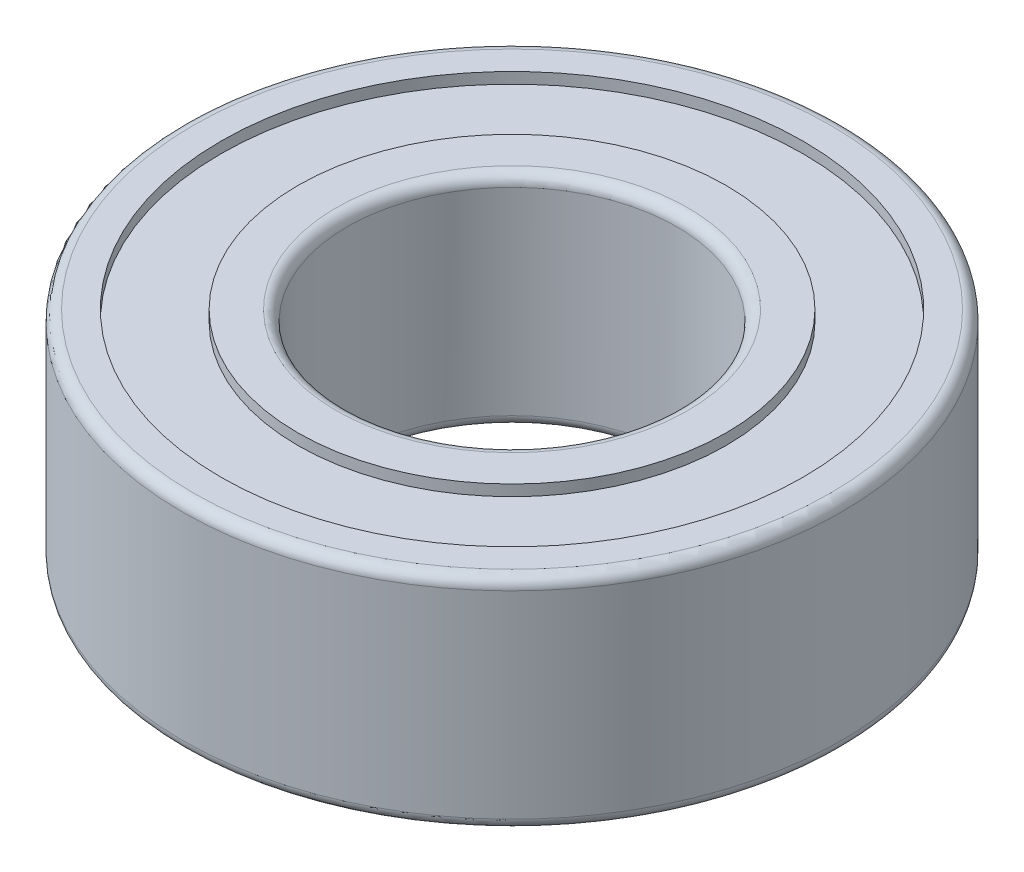
SolidWorks part; units mm, degrees
material "Plain Carbon Steel"
ref_plane "Front Plane" through (0, 0, 0) normal (0, 0, 1) x (1, 0, 0)
ref_plane "Top Plane" through (0, 0, 0) normal (0, 1, 0) x (1, 0, 0)
ref_plane "Right Plane" through (0, 0, 0) normal (1, 0, 0) x (0, 0, -1)
sketch "Sketch1" plane through (0, 0, 0) normal (1, 0, 0) x (0, 0, -1)
  line L0 (-6, 0) -> (-6, 2)
  line L1 (-6, 2) -> (-5.3, 2)
  line L2 (-5.3, 2) -> (-5.3, 1.8)
  line L3 (-5.3, 1.8) -> (-3.9, 1.8)
  line L4 (-3.9, 1.8) -> (-3.9, 2)
  line L5 (-3.9, 2) -> (-3, 2)
  line L6 (-3, 2) -> (-3, 0)
  line L7 (-3, 0) -> (-6, 0)
  line L8 (0, 15.2039) -> (0, -14.9126) construction
  point P11 (-5.65, 2)
  dimension "D1" = 6
  dimension "D2" = 12
  dimension "D3" = 2
  dimension "D4" = 0.2
  dimension "D5" = 0.7
  dimension "D6" = 0.9
revolve "Revolve1" add sketch "Sketch1" angle 360 about L8
fillet "Fillet1" radius 0.2 2 edges at (0, 2, 6) (0, 2, 3)
mirror "Mirror1" about plane through (0, 0, 0) normal (0, 1, 0) of "Fillet1", "Revolve1"
